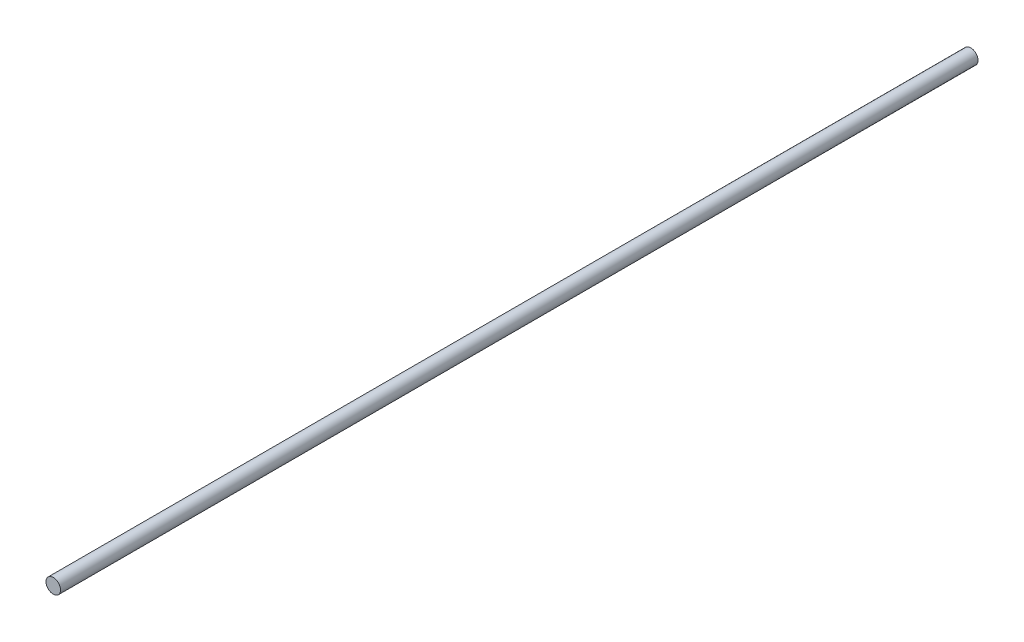
SolidWorks part; units mm, degrees
ref_plane "Front Plane" through (0, 0, 0) normal (0, 0, 1) x (1, 0, 0)
ref_plane "Top Plane" through (0, 0, 0) normal (0, 1, 0) x (1, 0, 0)
ref_plane "Right Plane" through (0, 0, 0) normal (1, 0, 0) x (0, 0, -1)
sketch "Sketch1" plane through (0, 0, 0) normal (0, 0, 1) x (1, 0, 0)
  circle A0 centre (0, 0) radius 3.175
  dimension "D1" = 6.35
extrude "Boss-Extrude1" add sketch "Sketch1" along normal blind 400
